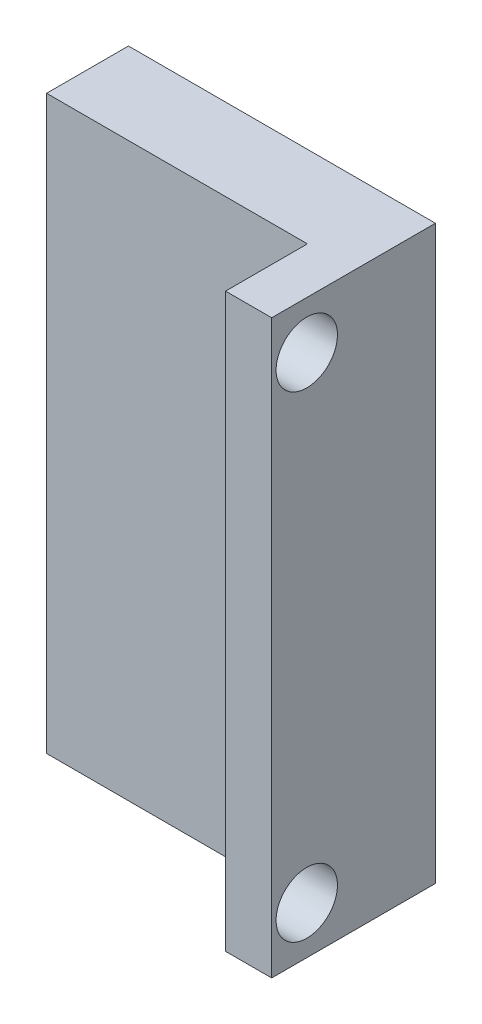
SolidWorks part; units mm, degrees
ref_plane "Front Plane" through (0, 0, 0) normal (0, 0, 1) x (1, 0, 0)
ref_plane "Top Plane" through (0, 0, 0) normal (0, 1, 0) x (1, 0, 0)
ref_plane "Right Plane" through (0, 0, 0) normal (1, 0, 0) x (0, 0, -1)
sketch "Sketch2" plane through (0, 0, 0) normal (0, 0, 1) x (1, 0, 0)
  line L1 (0, 0) -> (10, 0)
  line L2 (0, 0) -> (0, 10)
  line L3 (0, 10) -> (10, 10)
  line L4 (10, 0) -> (10, 10)
  dimension "D1" = 10
  dimension "D2" = 10
extrude "Boss-Extrude1" add sketch "Sketch2" along normal blind 158.8
sketch "Sketch3" plane through (10, 0, 0) normal (1, 0, 0) x (0, 0, -1)
  line L0 (0, 0) -> (0, 10) construction
  line L1 (-158.8, 10) -> (0, 10) construction
  circle A0 centre (-5, 5) radius 3.5
  dimension "D3" = 7
  dimension "D1" = 5
  dimension "D2" = 5
extrude "Boss-Extrude2" add sketch "Sketch3" along normal blind 8
sketch "Sketch4" plane through (0, 0, 158.8) normal (0, 0, 1) x (1, 0, 0)
  line L0 (0, 18.97) -> (0, -8.97)
  line L1 (0, -8.97) -> (15, -8.97)
  line L2 (15, -8.97) -> (15, 18.97)
  line L3 (15, 18.97) -> (0, 18.97)
  line L4 (0, 0) -> (10, 0) construction
  line L7 (10, 0) -> (10, 10) construction
  dimension "D1" = 270
  dimension "D2" = 27.94
  dimension "D3" = 10
  dimension "D4" = 8.97
  dimension "D5" = 15
extrude "Boss-Extrude4" add sketch "Sketch4" along normal blind 4
sketch "Sketch5" plane through (0, 0, 162.8) normal (0, 0, 1) x (1, 0, 0)
  line L0 (0, -8.97) -> (15, -8.97) construction
  line L1 (15, 18.97) -> (12.7455, 18.97)
  line L2 (15, 18.97) -> (15, -8.97)
  line L3 (15, -8.97) -> (12.7455, -8.97)
  line L4 (12.7455, 18.97) -> (12.7455, -8.97)
extrude "Boss-Extrude5" add sketch "Sketch5" along normal blind 4
sketch "Sketch6" plane through (12.7455, 0, 0) normal (-1, 0, 0) x (0, 0, 1)
  line L0 (162.8, 18.97) -> (162.8, -8.97) construction
  line L2 (166.8, -8.97) -> (162.8, -8.97) construction
  circle A0 centre (165.086, 16.6443) radius 1.5
  circle A1 centre (165.086, -6.645) radius 1.5
  dimension "D1" = 3
  dimension "D2" = 3
  dimension "D3" = 2.286
  dimension "D4" = 2.286
  dimension "D5" = 23.2893
  dimension "D6" = 2.325
extrude "Cut-Extrude1" cut sketch "Sketch6" against normal blind 40
sketch "Sketch7" plane through (0, 0, 0) normal (0, 0, -1) x (-1, 0, 0)
  line L1 (0, 0) -> (-23.1274, 0)
  line L2 (0, 0) -> (0, 13.3714)
  line L3 (0, 13.3714) -> (-23.1274, 13.3714)
  line L4 (-23.1274, 0) -> (-23.1274, 13.3714)
extrude "Cut-Extrude2" cut sketch "Sketch7" against normal up to surface (158.8 mm away) up to face at (6.25, 5, 158.8)
